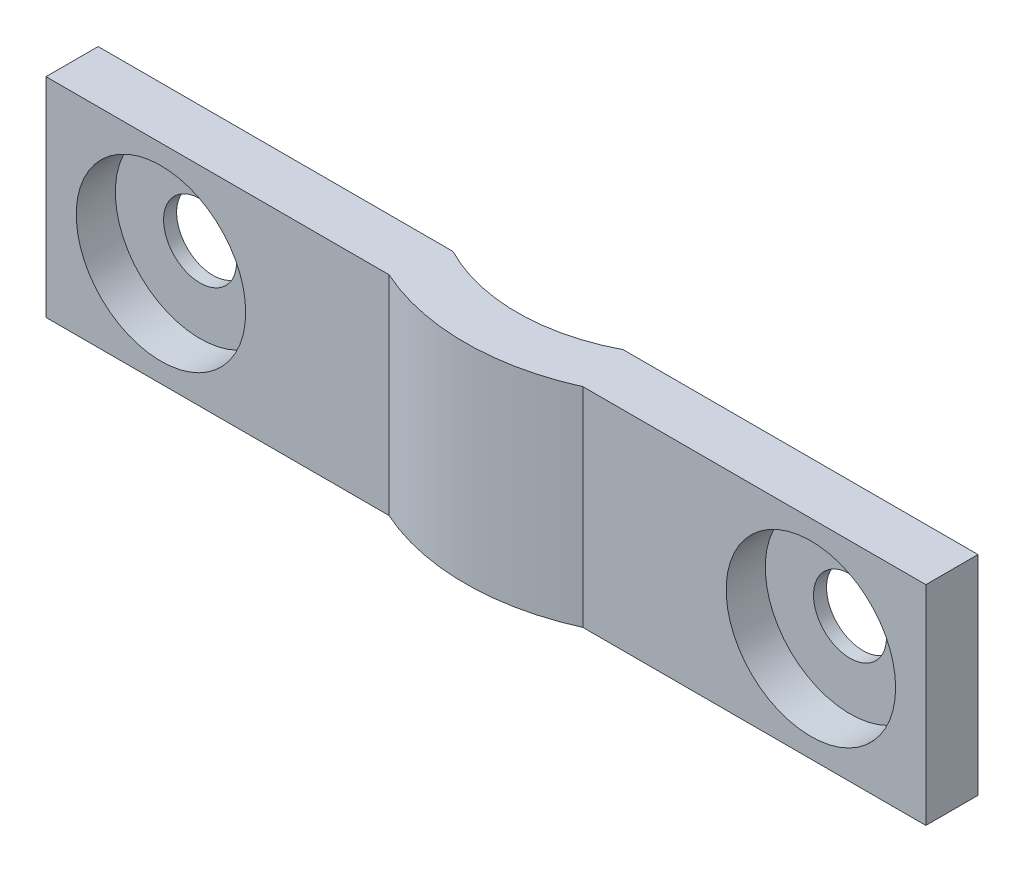
SolidWorks part; units mm, degrees
ref_plane "Alzado" through (0, 0, 0) normal (0, 0, 1) x (1, 0, 0)
ref_plane "Planta" through (0, 0, 0) normal (0, 1, 0) x (1, 0, 0)
ref_plane "Vista lateral" through (0, 0, 0) normal (1, 0, 0) x (0, 0, -1)
sketch "Croquis1" plane through (0, 0, 0) normal (0, 0, 1) x (1, 0, 0)
  line L0 (-58.8943, 45.9944) -> (-45.1443, 45.9944) construction
  line L1 (-57.6108, 49.9944) -> (-46.4277, 49.9944)
  line L2 (-57.6108, 41.9944) -> (-46.4277, 41.9944)
  line L3 (-58.8943, 49.9944) -> (-45.1443, 49.9944) construction
  line L4 (-58.8943, 41.9944) -> (-45.1443, 41.9944) construction
  line L5 (-57.6108, 49.9944) -> (-68.8943, 49.9944)
  line L6 (-68.8943, 49.9944) -> (-68.8943, 41.9944)
  line L7 (-68.8943, 41.9944) -> (-57.6108, 41.9944)
  line L8 (-46.4277, 49.9944) -> (-35.1443, 49.9944)
  line L9 (-35.1443, 49.9944) -> (-35.1443, 41.9944)
  line L10 (-35.1443, 41.9944) -> (-46.4277, 41.9944)
  line L11 (-52.0193, 52.8694) -> (-52.0193, 41.9944) construction
  circle A0 centre (-52.0193, 45.9944) radius 6.875 construction
  circle A1 centre (-52.0193, 45.9944) radius 6.875
  dimension "D3" = 10
  dimension "D4" = 10
  dimension "D1" = 4
  dimension "D2" = 4
sketch "Croquis2" plane through (0, 0, 0) normal (0, 0, 1) x (1, 0, 0)
  line L0 (-58.8943, 45.9944) -> (-45.1443, 45.9944)
  circle A1 centre (-52.0193, 45.9944) radius 6.875 construction
  circle A2 centre (-52.0193, 45.9944) radius 6.875 construction
ref_plane "Plano1" through (0, 45.9944, 0) normal (0, 1, 0) x (1, 0, 0)
sketch "Croquis3" plane through (0, 45.9944, 0) normal (0, 1, 0) x (1, 0, 0)
  line L0 (73.7179, 0) -> (-73.7179, 0) construction
  line L1 (73.7179, 0) -> (-73.7179, 0)
  line L2 (-52.0193, 13) -> (-45.2693, 13) construction
  line L3 (-57.6108, -2) -> (-57.6108, 0) construction
  line L4 (-52.0193, -2.5) -> (-52.0193, 11) construction
  line L8 (-58.8943, 0) -> (-58.8943, -2) construction
  circle A0 centre (-52.0193, 4.25) radius 6.75 construction
  circle A1 centre (-52.0193, 4.25) radius 6.75 construction
  circle A2 centre (-52.0193, 4.25) radius 8.0826 construction
  circle A3 centre (-52.0193, 4.25) radius 7.05 construction
  circle A4 centre (-52.0193, 6.25) radius 6.75 construction
  circle A5 centre (-52.0193, 6.25) radius 7.05
  circle A6 centre (-52.0193, 6.25) radius 9.05
  dimension "D1" = 0.3
  dimension "D2" = 2
  dimension "D6" = 13.5
  dimension "D7" = 13
  dimension "D3" = 2
  dimension "D4" = 1.2834
  dimension "D5" = 5.5916
  dimension "D8" = 0.3
  dimension "D9" = 2
extrude "Saliente-Extruir3" add sketch "Croquis3" along normal mid plane 8 separate body contours A3 L1 A2
ref_plane "Plano2" through (-68.8943, 0, 0) normal (1, 0, 0) x (0, 0, -1)
sketch "Croquis4" plane through (-68.8943, 0, 0) normal (1, 0, 0) x (0, 0, -1)
  line L1 (0, 49.9944) -> (-2, 49.9944)
  line L2 (0, 49.9944) -> (0, 41.9944)
  line L3 (0, 41.9944) -> (-2, 41.9944)
  line L4 (-2, 49.9944) -> (-2, 41.9944)
  dimension "D1" = 2
  dimension "D2" = 8
extrude "Saliente-Extruir5" add sketch "Croquis4" along normal up to surface (10.3298 mm away)
ref_plane "Plano3" through (-52.0193, 0, 0) normal (1, 0, 0) x (0, 0, -1)
mirror "Simetría1" about plane through (-52.0193, 0, 0) normal (1, 0, 0) of "Saliente-Extruir5"
sketch "Croquis5" plane through (0, 0, 2) normal (0, 0, 1) x (1, 0, 0)
  line L3 (-52.0193, 49.9944) -> (-52.0193, 41.9944)
  line L4 (-48.2991, 49.9944) -> (-55.7395, 49.9944) construction
  line L5 (-55.7395, 41.9944) -> (-48.2991, 41.9944) construction
  line L7 (-35.1443, 49.9944) -> (-35.1443, 41.9944) construction
  line L8 (-35.1443, 45.9944) -> (-48.2991, 45.9944) construction
  line L9 (-48.2991, 49.9944) -> (-48.2991, 41.9944) construction
  line L10 (-48.2991, 41.9944) -> (-35.1443, 41.9944) construction
  circle A3 centre (-39.5543, 45.9944) radius 3.25
  circle A5 centre (-64.4843, 45.9944) radius 3.25
  dimension "D1" = 4.41
  dimension "D2" = 6.5
  dimension "D3" = 4
extrude "Cortar-Extruir1" cut sketch "Croquis5" against normal blind 1.5
sketch "Croquis6" plane through (0, 0, 0.5) normal (0, 0, 1) x (1, 0, 0)
  line L3 (-35.1443, 45.9944) -> (-48.2991, 45.9944) construction
  line L4 (50, -95) -> (50, -70)
  line L5 (50, -70) -> (-50, -70)
  line L6 (-50, -70) -> (-50, -95)
  line L7 (-50, -95) -> (50, -95)
  line L8 (50, -95) -> (50, -70)
  line L9 (50, -70) -> (-50, -70)
  line L10 (-50, -70) -> (-50, -95)
  line L11 (-50, -95) -> (50, -95)
  line L13 (-35.1443, 49.9944) -> (-35.1443, 41.9944) construction
  line L14 (-52.0193, 49.9944) -> (-52.0193, 41.9944) construction
  line L18 (-55.7395, 41.9944) -> (-48.2991, 41.9944)
  line L19 (-48.2991, 41.9944) -> (-48.2991, 49.9944)
  line L20 (-48.2991, 49.9944) -> (-55.7395, 49.9944)
  line L22 (-55.7395, 41.9944) -> (-48.2991, 41.9944)
  line L24 (-48.2991, 49.9944) -> (-55.7395, 49.9944)
  line L30 (-48.2991, 41.9944) -> (-48.2991, 49.9944)
  line L32 (-55.7395, 49.9944) -> (-55.7395, 41.9944)
  line L33 (-55.7395, 49.9944) -> (-55.7395, 41.9944)
  circle A1 centre (-39.5543, 45.9944) radius 1.4
  circle A4 centre (-64.4843, 45.9944) radius 1.4
  point P4 (0, 0)
  point P8 (0, 0)
  dimension "D3" = 2.8
  dimension "D5" = 4.41
  dimension "D1" = 0
  dimension "D4" = 0
extrude "Cortar-Extruir2" cut sketch "Croquis6" against normal up to next contours A4
